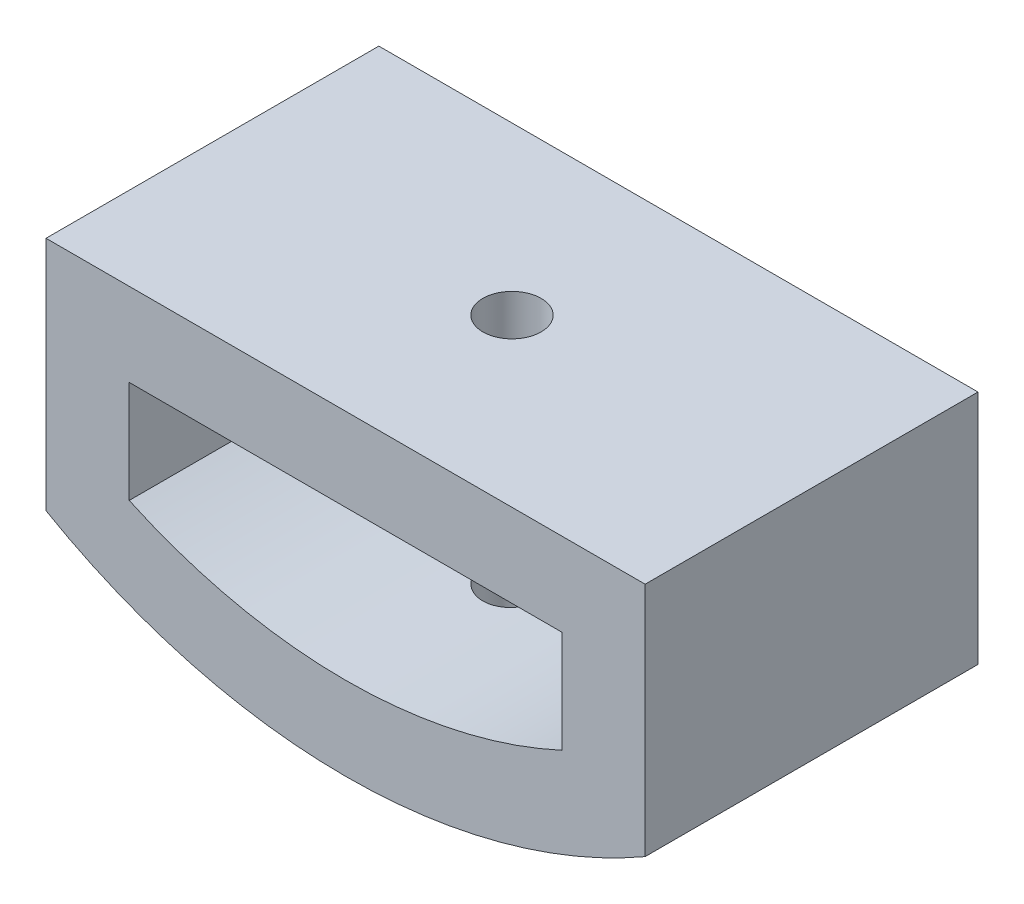
SolidWorks part; units mm, degrees
material "PET"
ref_plane "Front Plane" through (0, 0, 0) normal (0, 0, 1) x (1, 0, 0)
ref_plane "Top Plane" through (0, 0, 0) normal (0, 1, 0) x (1, 0, 0)
ref_plane "Right Plane" through (0, 0, 0) normal (1, 0, 0) x (0, 0, -1)
sketch "Sketch1" plane through (0, 0, 0) normal (0, 0, 1) x (1, 0, 0)
  line L0 (0, -15.5) -> (0, -8.5)
  line L1 (9, -8.5) -> (-9, -8.5)
  line L2 (-9, -8.5) -> (-9, -12.6194)
  line L3 (9, -8.5) -> (9, -12.6194)
  line L4 (6.5, -11) -> (6.5, -12.6194)
  line L5 (6.5, -11) -> (-6.5, -11)
  line L6 (-6.5, -11) -> (-6.5, -12.6194)
  line L7 (-6.5, -12.6194) -> (-6.5, -14.0712)
  line L8 (6.5, -12.6194) -> (6.5, -14.0712)
  line L9 (-9, -12.6194) -> (-9, -15.5885)
  line L10 (9, -12.6194) -> (9, -15.5885)
  circle A0 centre (0, 0) radius 18
  circle A1 centre (0, 0) radius 15.5
  point P10 (0, -8.5)
  dimension "D1" = 36
  dimension "D3" = 7
  dimension "D4" = 18
  dimension "D2" = 2.5
  dimension "D5" = 2.5
extrude "Boss-Extrude1" add sketch "Sketch1" along normal blind 10 contours A1 L9 A0 L10 | L2 A1 L7 L6 L5 L0 L1 | L8 A1 L3 L1 L0 L5 L4
sketch "Sketch2" plane through (0, 0, 0) normal (0, 1, 0) x (1, 0, 0)
  line L1 (9, 0) -> (-9, 0) construction
  circle A0 centre (0, -5) radius 0.875
  point P4 (0, 0)
  dimension "D1" = 1.75
  dimension "D2" = 5
extrude "Cut-Extrude3" cut sketch "Sketch2" against normal blind 23
